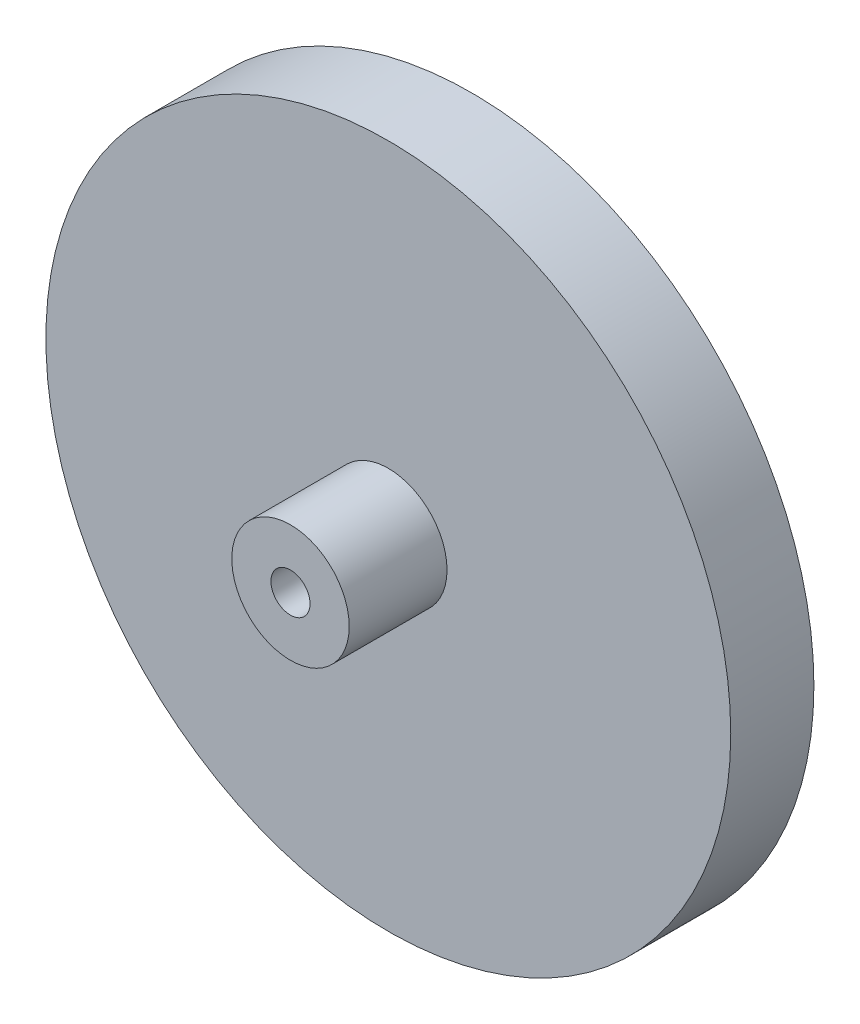
SolidWorks part; units mm, degrees
ref_plane "Front Plane" through (0, 0, 0) normal (0, 0, 1) x (1, 0, 0)
ref_plane "Top Plane" through (0, 0, 0) normal (0, 1, 0) x (1, 0, 0)
ref_plane "Right Plane" through (0, 0, 0) normal (1, 0, 0) x (0, 0, -1)
sketch "Sketch1" plane through (0, 0, 0) normal (0, 0, 1) x (1, 0, 0)
  circle A0 centre (0, 0) radius 35
  circle A1 centre (0, 0) radius 2
  dimension "D1" = 70
  dimension "D2" = 4
extrude "Boss-Extrude1" add sketch "Sketch1" along normal blind 8.5
sketch "Sketch2" plane through (0, 0, 8.5) normal (0, 0, 1) x (1, 0, 0)
  circle A0 centre (0, 0) radius 6
  circle A1 centre (0, 0) radius 2
  circle A2 centre (0, 0) radius 2 construction
  dimension "D1" = 12
extrude "Boss-Extrude2" add sketch "Sketch2" along normal blind 10
